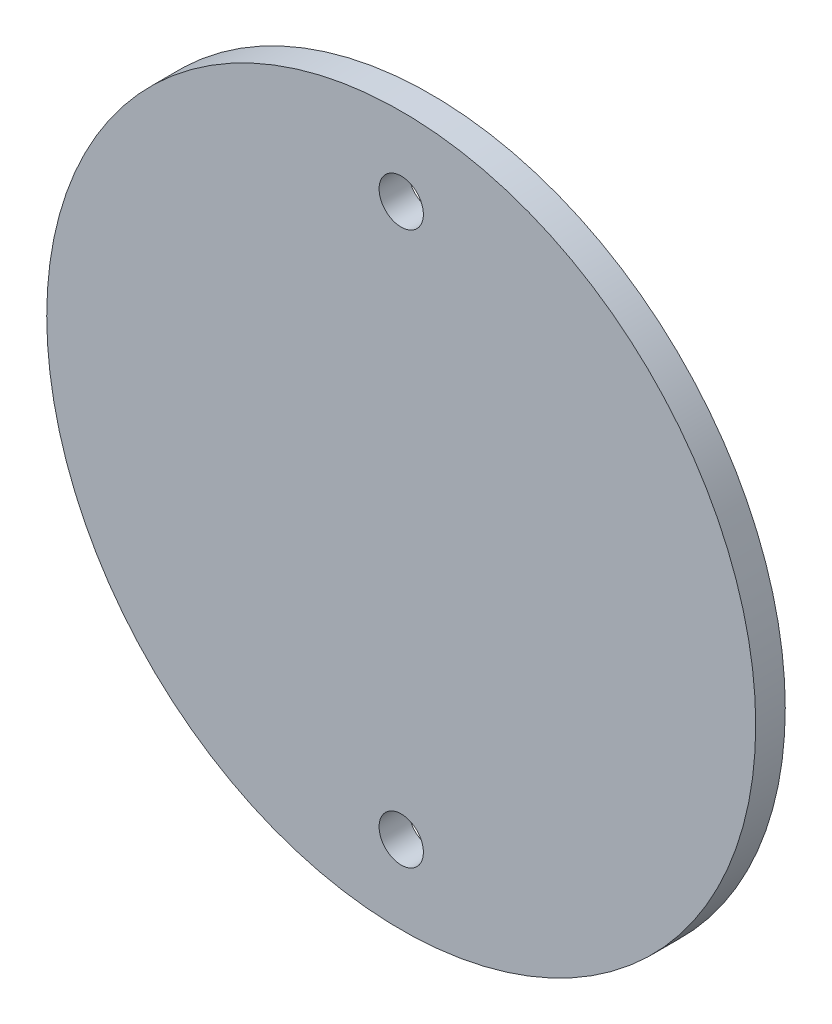
SolidWorks part; units mm, degrees
ref_plane "Front Plane" through (0, 0, 0) normal (0, 0, 1) x (1, 0, 0)
ref_plane "Top Plane" through (0, 0, 0) normal (0, 1, 0) x (1, 0, 0)
ref_plane "Right Plane" through (0, 0, 0) normal (1, 0, 0) x (0, 0, -1)
sketch "Sketch1" plane through (0, 0, 0) normal (0, 0, 1) x (1, 0, 0)
  line L0 (0, 59.3725) -> (0, -59.3725) construction
  circle A0 centre (0, 0) radius 76.2
  circle A1 centre (0, 59.3725) radius 4.7625
  circle A2 centre (0, -59.3725) radius 4.7625
  dimension "D1" = 152.4
  dimension "D3" = 9.525
  dimension "D2" = 118.745
extrude "Boss-Extrude1" add sketch "Sketch1" along normal blind 6.35
